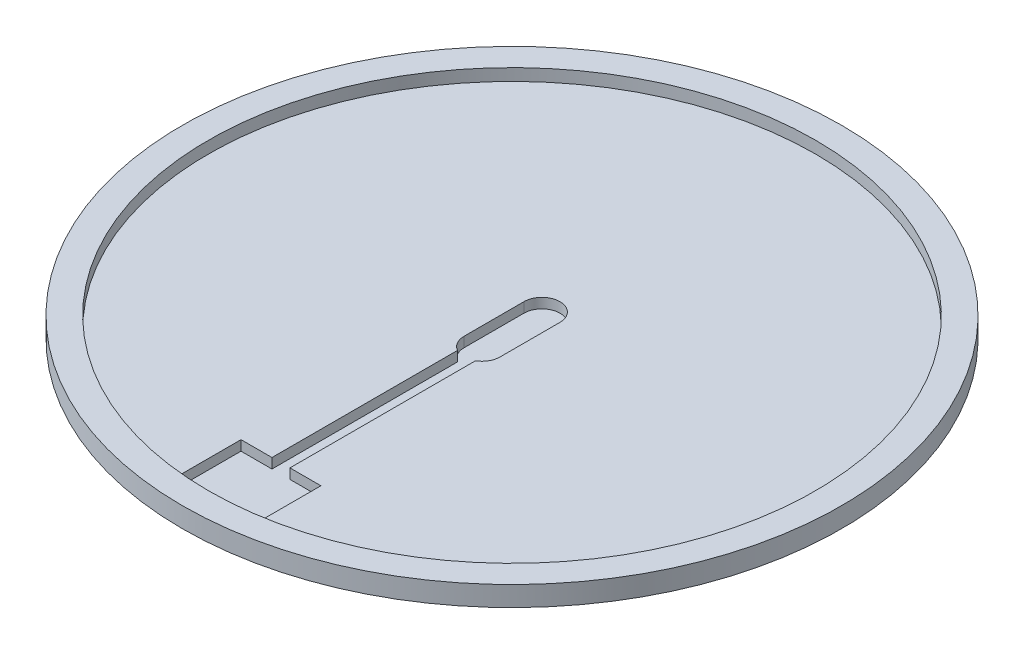
SolidWorks part; units mm, degrees
ref_plane "Front Plane" through (0, 0, 0) normal (0, 0, 1) x (1, 0, 0)
ref_plane "Top Plane" through (0, 0, 0) normal (0, 1, 0) x (1, 0, 0)
ref_plane "Right Plane" through (0, 0, 0) normal (1, 0, 0) x (0, 0, -1)
sketch "Sketch1" plane through (0, 0, 0) normal (0, 1, 0) x (1, 0, 0)
  circle A0 centre (0, 0) radius 150
  dimension "D1" = 300
sketch "Sketch2" plane through (0, 0, 0) normal (0, 1, 0) x (1, 0, 0)
  circle A2 centre (0, 0) radius 165
  circle A3 centre (0, 0) radius 165
  dimension "D1" = 15
extrude "Boss-Extrude1" add sketch "Sketch2" along normal blind 13
sketch "Sketch3" plane through (0, 0, 0) normal (0, -1, 0) x (1, 0, 0)
  circle A1 centre (0, 0) radius 165 construction
  circle A2 centre (0, 0) radius 149
  circle A3 centre (0, 0) radius 149
  circle A4 centre (0, 0) radius 165
  dimension "D1" = 1
extrude "Cut-Extrude1" cut sketch "Sketch3" against normal blind 3
sketch "Sketch4" plane through (0, 13, 0) normal (0, 1, 0) x (1, 0, 0)
  circle A2 centre (0, 0) radius 152
  circle A3 centre (0, 0) radius 152
  dimension "D1" = 2
extrude "Cut-Extrude2" cut sketch "Sketch4" against normal blind 6
sketch "Sketch5" plane through (0, 7, 0) normal (0, 1, 0) x (1, 0, 0)
  line L0 (-4.5, -115.6785) -> (-4.5, -22.7942)
  line L1 (0, -15) -> (0, 15) construction
  line L2 (9, -15) -> (9, 15)
  line L3 (-23.5598, 0) -> (0, 0) construction
  line L4 (-9, -15) -> (-9, 15)
  line L5 (9, -15) -> (-9, 15) construction
  line L6 (9, 15) -> (-9, -15) construction
  line L7 (0, 15) -> (0, 39.722) construction
  line L8 (-4.5, -115.6785) -> (-20, -115.6785)
  line L9 (-20, -115.6785) -> (-20, -150.6785)
  line L10 (20, -115.6785) -> (20, -150.6785)
  line L11 (4.5, -115.6785) -> (20, -115.6785)
  line L12 (4.5, -115.6785) -> (4.5, -22.7942)
  line L13 (-9, -15) -> (0, -15) construction
  arc A0 (-20, -150.6785) -> (20, -150.6785) centre (0, 0) ccw
  circle A1 centre (0, 0) radius 152 construction
  arc A2 (-9, 15) -> (9, 15) centre (0, 15) cw
  arc A3 (-9, -15) -> (-4.5, -22.7942) centre (0, -15) ccw
  arc A4 (4.5, -22.7942) -> (9, -15) centre (0, -15) ccw
  point P0 (0, 0)
  dimension "D1" = 18
  dimension "D2" = 30
  dimension "D3" = 9
  dimension "D4" = 40
  dimension "D5" = 35
extrude "Cut-Extrude3" cut sketch "Sketch5" against normal blind 5
